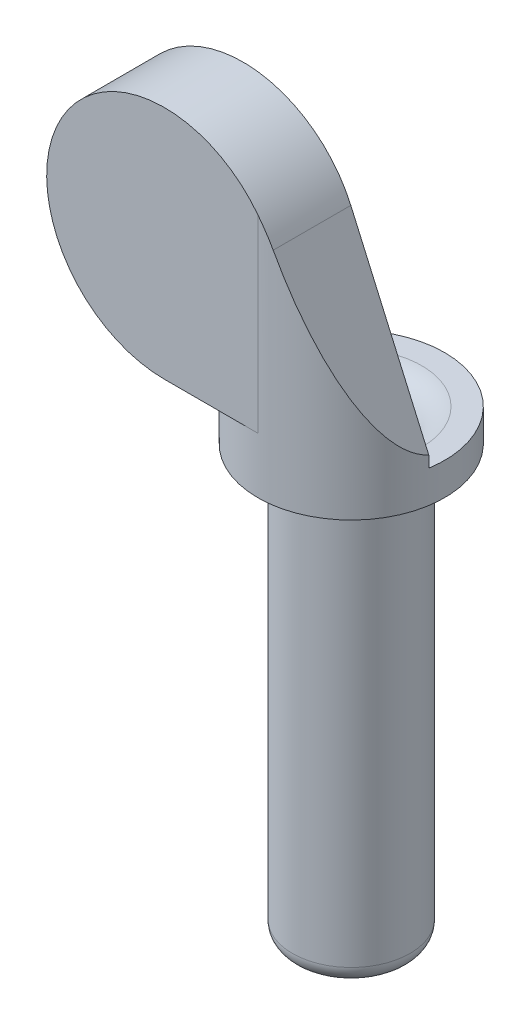
SolidWorks part; units mm, degrees
ref_plane "前视基准面" through (0, 0, 0) normal (0, 0, 1) x (1, 0, 0)
ref_plane "上视基准面" through (0, 0, 0) normal (0, 1, 0) x (1, 0, 0)
ref_plane "右视基准面" through (0, 0, 0) normal (1, 0, 0) x (0, 0, -1)
sketch "草图1" plane through (0, 0, 0) normal (0, 1, 0) x (1, 0, 0)
  line L0 (0, 0) -> (0, 4.3268) construction
  line L1 (0, 0) -> (6.0935, 0) construction
  circle A0 centre (0, 0) radius 2
  dimension "D1" = 4
extrude "凸台-拉伸1" add sketch "草图1" along normal blind 16
sketch "草图2" plane through (0, 0, 0) normal (0, 0, 1) x (1, 0, 0)
  line L0 (-2, 19.9066) -> (-2, 24.3235) construction
  line L1 (-2, 16) -> (-2, 0) construction
  line L2 (-2.327, 16) -> (-3.6912, 16) construction
  line L3 (2, 16) -> (-2, 16) construction
  line L4 (3.175, 16) -> (0.4863, 22.1109)
  line L6 (0, 19.5869) -> (0, 22.2425) construction
  line L7 (3.175, 16) -> (-3.175, 16)
  line L8 (-3.175, 16) -> (-3.175, 16.5)
  arc A0 (0.4863, 22.1109) -> (-3.175, 16.5) centre (-3.175, 20.5) ccw
  dimension "D1" = 4.5
  dimension "D2" = 8
  dimension "D3" = 3.175
  dimension "D4" = 3.175
extrude "凸台-拉伸2" add sketch "草图2" along normal blind 3.175
sketch "草图4" plane through (0, 0, 0) normal (0, 0, -1) x (-1, 0, 0)
  circle A0 centre (3.175, 20.5) radius 1.65
  dimension "D1" = 3.3
extrude "切除-拉伸6" cut sketch "草图4" against normal blind 2.5
sketch "草图5" plane through (0, 16, 0) normal (0, 1, 0) x (1, 0, 0)
  line L1 (3.175, 0) -> (-7.475, 0)
  line L2 (3.175, 0) -> (3.175, -0.5)
  line L3 (3.175, -0.5) -> (-7.475, -0.5)
  line L4 (-7.475, 0) -> (-7.475, -0.5)
  dimension "D1" = 0.5
  dimension "D2" = 10.65
extrude "切除-拉伸8" cut sketch "草图5" along normal through all
fillet "圆角3" radius 0.6 1 edges at (0, 0, 2)
sketch "草图7" plane through (0, 16, 0) normal (0, 1, 0) x (1, 0, 0)
  circle A0 centre (0, 0) radius 3.175
  dimension "D1" = 6.35
extrude "凸台-拉伸3" add sketch "草图7" against normal blind 1.4
fillet "圆角5" radius 0.3 1 edges at (-4.825, 20.5, 0.5)
sketch "草图10" plane through (0, 0, 0) normal (0, -1, 0) x (1, 0, 0)
  line L0 (-3.1354, 0.5) -> (1.6694, 0.5) construction
  line L3 (-7.175, 0.5) -> (0.4863, 0.5) construction
  line L6 (-1.3077, 0.5) -> (1.3077, 0.5)
  arc A0 (-1.3077, 0.5) -> (1.3077, 0.5) centre (0, 0) ccw
  circle A2 centre (0, 0) radius 3.175 construction
  dimension "D1" = 1.4
extrude "切除-拉伸9" cut sketch "草图10" against normal through all both and the other way through all
sketch "草图11" plane through (0, 16, 0) normal (0, -1, 0) x (1, 0, 0)
  line L4 (3.175, 3.175) -> (0, 3.175)
  line L5 (3.175, 3.175) -> (4.0086, 0.5)
  line L6 (4.0086, 0.5) -> (3.1354, 0.5)
  arc A2 (0, 3.175) -> (3.1354, 0.5) centre (0, 0) cw
extrude "切除-拉伸10" cut sketch "草图11" against normal through all
sketch "草图12" plane through (0, 16, 0) normal (0, 1, 0) x (1, 0, 0)
  line L0 (-3.1354, -0.5) -> (3.1354, -0.5)
  arc A0 (-3.1354, -0.5) -> (3.1354, -0.5) centre (0, 0) cw
extrude "切除-拉伸11" cut sketch "草图12" against normal blind 0.3
fillet "圆角6" radius 1 1 edges at (0, 15.7, -1.4)
sketch "草图13" plane through (0, 16, 0) normal (0, -1, 0) x (1, 0, 0)
  line L0 (-3.1354, 0.5) -> (-3.175, 0.5)
  line L1 (-3.175, 0.5) -> (-3.175, 3.175)
  line L2 (-3.175, 3.175) -> (0, 3.175)
  circle A0 centre (0, 0) radius 3.175 construction
  arc A1 (0, 3.175) -> (-3.1354, 0.5) centre (0, 0) ccw construction
  arc A2 (0, 3.175) -> (-3.1354, 0.5) centre (0, 0) ccw
extrude "切除-拉伸12" cut sketch "草图13" against normal blind 0.5
